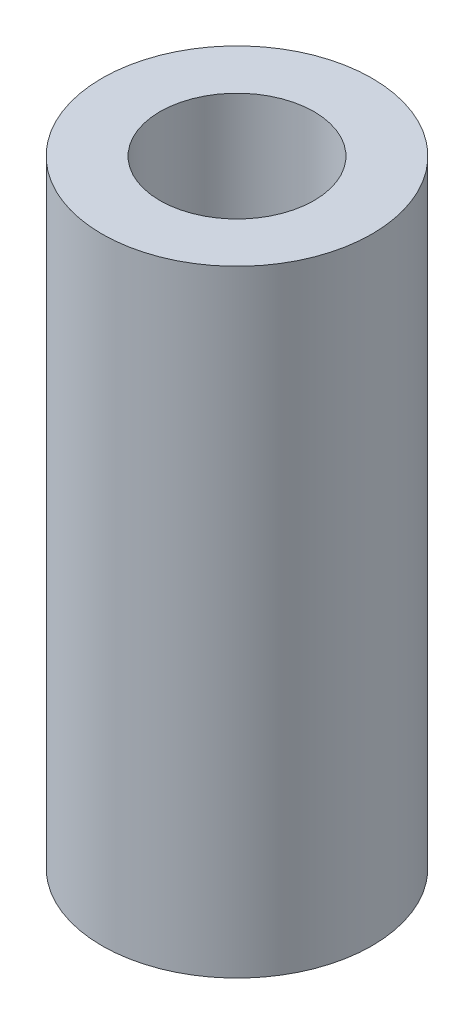
SolidWorks part; units mm, degrees
ref_plane "Front Plane" through (0, 0, 0) normal (0, 0, 1) x (1, 0, 0)
ref_plane "Top Plane" through (0, 0, 0) normal (0, 1, 0) x (1, 0, 0)
ref_plane "Right Plane" through (0, 0, 0) normal (1, 0, 0) x (0, 0, -1)
sketch "Sketch1" plane through (0, 0, 0) normal (0, 1, 0) x (1, 0, 0)
  circle A0 centre (0, 0) radius 3.175
  circle A1 centre (0, 0) radius 5.5626
  dimension "D1" = 6.35
  dimension "D2" = 11.1252
extrude "Boss-Extrude1" add sketch "Sketch1" along normal blind 25.4
